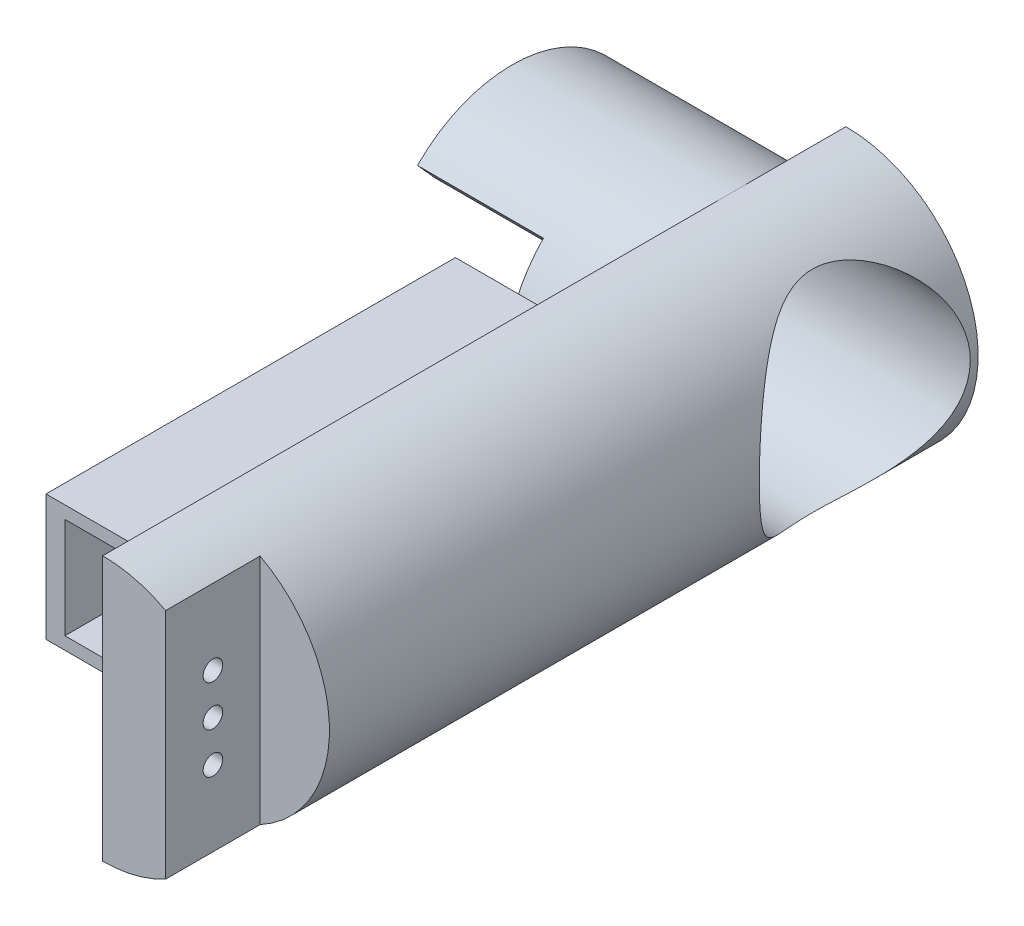
SolidWorks part; units mm, degrees
ref_plane "前视基准面" through (0, 0, 0) normal (0, 0, 1) x (1, 0, 0)
ref_plane "上视基准面" through (0, 0, 0) normal (0, 1, 0) x (1, 0, 0)
ref_plane "右视基准面" through (0, 0, 0) normal (1, 0, 0) x (0, 0, -1)
sketch "Sketch1" plane through (0, 0, 0) normal (1, 0, 0) x (0, 0, -1)
  circle A0 centre (0, 0) radius 21
  dimension "D1" = 42
extrude "Boss-Extrude1" add sketch "Sketch1" along normal blind 35 contours A0
sketch "Sketch4" plane through (0, 0, 0) normal (0, 0, 1) x (1, 0, 0)
  line L0 (35, -21) -> (35, 21) construction
  line L1 (35, 21) -> (35, -21)
  arc A0 (35, 21) -> (35, -21) centre (35, 0) cw
extrude "Boss-Extrude2" add sketch "Sketch4" along normal blind 100 and the other way blind 18
sketch "Sketch5" plane through (0, 0, 100) normal (0, 0, 1) x (1, 0, 0)
  line L0 (35, 21) -> (35, -21) construction
  line L1 (35, 21) -> (35, -21) construction
  line L2 (45, -18.4662) -> (45, 18.4662)
  arc A0 (45, 18.4662) -> (45, -18.4662) centre (35, 0) cw
  arc A2 (35, -21) -> (35, 21) centre (35, 0) ccw construction
  dimension "D1" = 10
extrude "Cut-Extrude2" cut sketch "Sketch5" against normal blind 15
sketch "Sketch7" plane through (35, 0, 0) normal (-1, 0, 0) x (0, 0, 1)
  line L1 (97, 15) -> (88, 15)
  line L2 (97, 15) -> (97, -15)
  line L3 (97, -15) -> (88, -15)
  line L4 (88, 15) -> (88, -15)
  line L8 (0, 21) -> (100, 21) construction
  line L9 (0, -21) -> (100, -21) construction
  line L10 (100, 21) -> (100, -21) construction
  dimension "D1" = 6
  dimension "D2" = 6
  dimension "D3" = 3
  dimension "D4" = 12
extrude "Cut-Extrude3" cut sketch "Sketch7" against normal blind 7
sketch "Sketch8" plane through (42, 0, 0) normal (-1, 0, 0) x (0, 0, 1)
  line L0 (92.5, 15) -> (92.5, -15) construction
  line L1 (97, 15) -> (88, 15) construction
  line L2 (88, -15) -> (97, -15) construction
  circle A0 centre (92.5, 6.5) radius 1.55
  circle A1 centre (92.5, 0) radius 1.55
  circle A2 centre (92.5, -6.5) radius 1.55
  dimension "D1" = 3.1
  dimension "D2" = 6.5
  dimension "D3" = 6.5
extrude "Cut-Extrude4" cut sketch "Sketch8" against normal blind 7
sketch "Sketch9" plane through (0, 0, 0) normal (-1, 0, 0) x (0, 0, 1)
  circle A0 centre (0, 0) radius 16.75
  dimension "D1" = 33.5
extrude "Cut-Extrude5" cut sketch "Sketch9" against normal blind 20
sketch "Sketch10" plane through (0, 0, 0) normal (-1, 0, 0) x (0, 0, 1)
  line L0 (15.0213, 14.6751) -> (12.1738, 11.5048)
  line L1 (11.5048, -12.1738) -> (14.6751, -15.0213)
  line L2 (0, 21) -> (100, 21) construction
  arc A0 (12.1738, 11.5048) -> (11.5048, -12.1738) centre (0, 0) cw
  circle A1 centre (0, 0) radius 16.75 construction
  arc A2 (15.0213, 14.6751) -> (14.6751, -15.0213) centre (0, 0) cw
  circle A3 centre (0, 0) radius 21 construction
  dimension "D1" = 4.2614
  dimension "D2" = 4.2614
  dimension "D3" = 6.3249
extrude "Cut-Extrude6" cut sketch "Sketch10" against normal blind 20
sketch "Sketch11" plane through (20, 0, 0) normal (-1, 0, 0) x (0, 0, 1)
  line L0 (0, 16.75) -> (0, -16.75) construction
  line L1 (-16.75, 0) -> (16.75, 0) construction
  line L2 (0, 0) -> (-11.844, 11.844) construction
  line L3 (0, 0) -> (11.844, -11.844) construction
  line L4 (0, 0) -> (-11.844, -11.844) construction
  line L5 (0, 0) -> (11.844, 11.844) construction
  arc A0 (12.1738, 11.5048) -> (11.5048, -12.1738) centre (0, 0) ccw construction
  arc A1 (12.1738, 11.5048) -> (11.5048, -12.1738) centre (0, 0) ccw construction
  circle A5 centre (-8.4853, 8.4853) radius 1.65
  circle A6 centre (8.4853, 8.4853) radius 1.65
  circle A7 centre (8.4853, -8.4853) radius 1.65
  circle A8 centre (-8.4853, -8.4853) radius 1.65
  arc A10 (12.1738, 11.5048) -> (11.5048, -12.1738) centre (0, 0) ccw construction
  dimension "D2" = 3.3
  dimension "D3" = 12
  dimension "D5" = 12
  dimension "D6" = 12
  dimension "D7" = 16.75
  dimension "D1" = 45
  dimension "D4" = 12
  dimension "D8" = 33.5
sketch "Sketch12" plane through (35, 0, 0) normal (-1, 0, 0) x (0, 0, 1)
  circle A0 centre (0, 0) radius 16.75
extrude "Cut-Extrude9" cut sketch "Sketch11" against normal blind 25
extrude "Cut-Extrude8" cut sketch "Sketch12" against normal blind 25 and the other way blind 10
sketch "Sketch14" plane through (0, 0, 0) normal (-1, 0, 0) x (0, 0, 1)
  line L0 (-14.711, 14.9862) -> (-11.8291, 11.8589)
  line L1 (-11.8589, -11.8291) -> (-14.9862, -14.711)
  arc A0 (-14.711, 14.9862) -> (-14.9862, -14.711) centre (0, 0) ccw
  arc A1 (0, 21) -> (-18, 10.8167) centre (0, 0) ccw construction
  arc A2 (-11.8291, 11.8589) -> (-11.8589, -11.8291) centre (0, 0) ccw
  arc A3 (12.1738, 11.5048) -> (11.5048, -12.1738) centre (0, 0) ccw construction
  dimension "D1" = 4.2527
  dimension "D2" = 4.2527
  dimension "D3" = 2.8818
extrude "Cut-Extrude10" cut sketch "Sketch14" against normal blind 20
sketch "Sketch15" plane through (35, 0, 0) normal (-1, 0, 0) x (0, 0, 1)
  line L0 (0, -21) -> (100, -21) construction
  line L1 (85, 10) -> (20, 10)
  line L2 (85, 10) -> (85, -10)
  line L3 (85, -10) -> (20, -10)
  line L4 (20, 10) -> (20, -10)
  line L5 (-18, 21) -> (-18, 10.8167) construction
  line L6 (100, 21) -> (100, -21) construction
  dimension "D1" = 20
  dimension "D2" = 11
  dimension "D3" = 38
  dimension "D4" = 15
extrude "Boss-Extrude3" add sketch "Sketch15" along normal blind 24
sketch "Sketch16" plane through (0, 0, 85) normal (0, 0, 1) x (1, 0, 0)
  line L0 (11, 0) -> (34.1417, 0) construction
  line L1 (11, -10) -> (11, 10) construction
  line L3 (27, -8) -> (14, -8)
  line L4 (27, -8) -> (27, 8)
  line L5 (27, 8) -> (14, 8)
  line L6 (14, -8) -> (14, 8)
  line L7 (27, -8) -> (14, 8) construction
  line L8 (27, 8) -> (14, -8) construction
  point P4 (20.5, 0)
  dimension "D1" = 16
  dimension "D2" = 3
  dimension "D3" = 16
extrude "Cut-Extrude11" cut sketch "Sketch16" against normal up to surface (65 mm away) up to face at (25.25, 0, 20)
